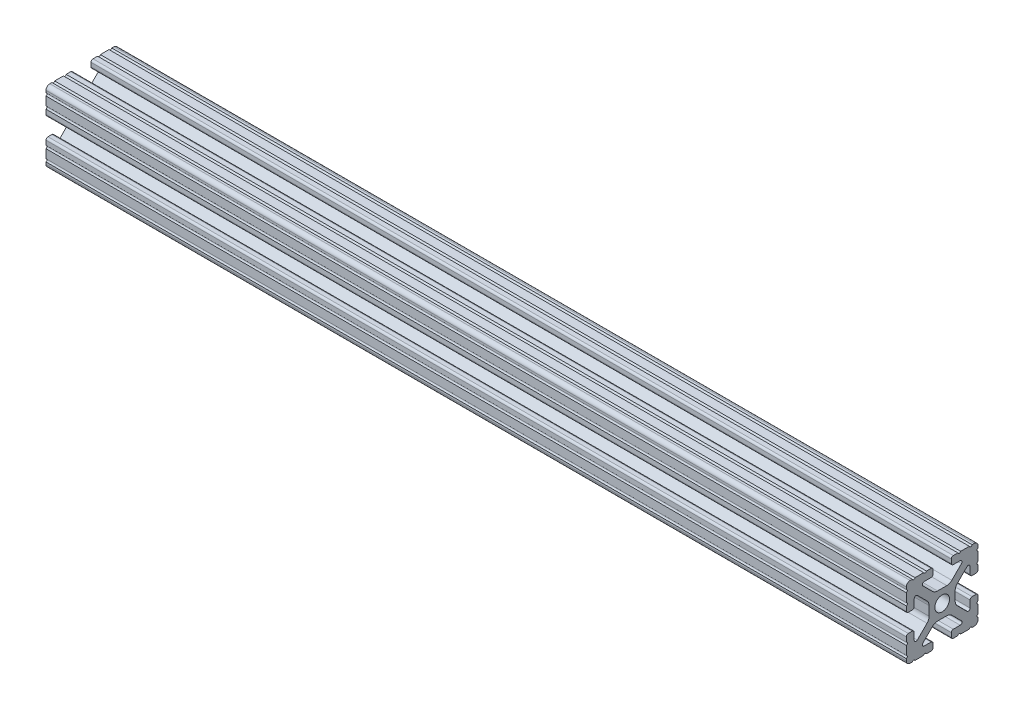
SolidWorks part; units mm, degrees
ref_plane "Front Plane" through (0, 0, 0) normal (0, 0, 1) x (1, 0, 0)
ref_plane "Top Plane" through (0, 0, 0) normal (0, 1, 0) x (1, 0, 0)
ref_plane "Right Plane" through (0, 0, 0) normal (1, 0, 0) x (0, 0, -1)
sketch "Sketch3"
sketch "Sketch2" plane through (0, 0, 0) normal (1, 0, 0) x (0, 0, -1)
  line L0 (16.1207, 7.3347) -> (19.544, 3.9114)
  line L1 (17.3256, 11.0651) -> (17.3256, 14.3349)
  line L2 (18.0653, 16.1207) -> (21.4886, 19.544)
  line L3 (22.598, 16.6362) -> (22.598, 19.0845)
  line L4 (24.7023, 15.9385) -> (23.2956, 15.9385)
  line L6 (2.1006, 25.4) -> (1.3474, 25.4)
  line L7 (16.6362, 2.802) -> (19.0845, 2.802)
  line L8 (0.6977, 15.9385) -> (2.1044, 15.9385)
  line L9 (2.802, 16.6362) -> (2.802, 19.0845)
  line L10 (0, 16.6362) -> (0, 18.2699)
  line L11 (8.0744, 11.0651) -> (8.0744, 14.3349)
  line L12 (7.3347, 16.1207) -> (3.9114, 19.544)
  line L13 (0, 19.2426) -> (0, 22.318)
  line L14 (0, 23.2994) -> (0, 24.0526)
  line L15 (6.1574, 25.4) -> (3.082, 25.4)
  line L16 (8.7638, 25.4) -> (7.1301, 25.4)
  line L17 (9.4615, 24.7023) -> (9.4615, 23.2956)
  line L18 (8.7638, 22.598) -> (6.3155, 22.598)
  line L19 (9.2793, 18.0653) -> (5.856, 21.4886)
  line L20 (14.3349, 17.3256) -> (11.0651, 17.3256)
  line L22 (25.4, 16.6362) -> (25.4, 18.2699)
  line L23 (25.4, 19.2426) -> (25.4, 22.318)
  line L24 (25.4, 23.2994) -> (25.4, 24.0526)
  line L25 (23.2994, 25.4) -> (24.0526, 25.4)
  line L26 (19.2426, 25.4) -> (22.318, 25.4)
  line L27 (16.6362, 25.4) -> (18.2699, 25.4)
  line L28 (15.9385, 24.7023) -> (15.9385, 23.2956)
  line L29 (16.6362, 22.598) -> (19.0845, 22.598)
  line L30 (16.1207, 18.0653) -> (19.544, 21.4886)
  line L31 (15.9385, 0.6977) -> (15.9385, 2.1044)
  line L32 (16.6362, 0) -> (18.2699, 0)
  line L33 (19.2426, 0) -> (22.318, 0)
  line L34 (23.2994, 0) -> (24.0526, 0)
  line L35 (25.4, 2.1006) -> (25.4, 1.3474)
  line L36 (25.4, 6.1574) -> (25.4, 3.082)
  line L37 (25.4, 8.7638) -> (25.4, 7.1301)
  line L38 (14.3349, 8.0744) -> (11.0651, 8.0744)
  line L39 (9.2793, 7.3347) -> (5.856, 3.9114)
  line L40 (8.7638, 2.802) -> (6.3155, 2.802)
  line L41 (9.4615, 0.6977) -> (9.4615, 2.1044)
  line L42 (8.7638, 0) -> (7.1301, 0)
  line L43 (6.1574, 0) -> (3.082, 0)
  line L44 (0, 2.1006) -> (0, 1.3474)
  line L45 (0, 6.1574) -> (0, 3.082)
  line L46 (7.3347, 9.2793) -> (3.9114, 5.856)
  line L47 (0, 8.7638) -> (0, 7.1301)
  line L48 (2.802, 8.7638) -> (2.802, 6.3155)
  line L49 (0.6977, 9.4615) -> (2.1044, 9.4615)
  line L50 (2.1006, 0) -> (1.3474, 0)
  line L51 (24.7023, 9.4615) -> (23.2956, 9.4615)
  line L52 (22.598, 8.7638) -> (22.598, 6.3155)
  line L53 (18.0653, 9.2793) -> (21.4886, 5.856)
  circle A0 centre (12.7, 12.7) radius 2.6035
  arc A1 (7.3347, 16.1207) -> (8.0744, 14.3349) centre (5.5489, 14.3349) cw
  arc A2 (2.802, 19.0845) -> (3.9114, 19.544) centre (3.4519, 19.0845) cw
  arc A3 (2.802, 16.6362) -> (2.1044, 15.9385) centre (2.1044, 16.6362) cw
  arc A4 (0, 16.6362) -> (0.6977, 15.9385) centre (0.6977, 16.6362) ccw
  arc A5 (-0.0204, 18.2642) -> (-0.0101, 19.2455) centre (-0.1467, 18.7562) ccw
  arc A6 (0, 22.318) -> (0, 23.2994) centre (-0.1315, 22.8087) ccw
  arc A7 (0, 24.0526) -> (1.3474, 25.4) centre (1.3474, 24.0526) cw
  arc A8 (3.082, 25.4) -> (2.1006, 25.4) centre (2.5913, 25.5315) cw
  arc A9 (7.1358, 25.4204) -> (6.1545, 25.4101) centre (6.6438, 25.5467) cw
  arc A10 (8.7638, 25.4) -> (9.4615, 24.7023) centre (8.7638, 24.7023) cw
  arc A11 (8.7638, 22.598) -> (9.4615, 23.2956) centre (8.7638, 23.2956) ccw
  arc A12 (6.3155, 22.598) -> (5.856, 21.4886) centre (6.3155, 21.9481) ccw
  arc A13 (9.2793, 18.0653) -> (11.0651, 17.3256) centre (11.0651, 19.8511) ccw
  arc A14 (18.0653, 16.1207) -> (17.3256, 14.3349) centre (19.8511, 14.3349) ccw
  arc A15 (22.598, 19.0845) -> (21.4886, 19.544) centre (21.9481, 19.0845) ccw
  arc A16 (22.598, 16.6362) -> (23.2956, 15.9385) centre (23.2956, 16.6362) ccw
  arc A17 (25.4, 16.6362) -> (24.7023, 15.9385) centre (24.7023, 16.6362) cw
  arc A18 (25.4204, 18.2642) -> (25.4101, 19.2455) centre (25.5467, 18.7562) cw
  arc A19 (25.4, 22.318) -> (25.4, 23.2994) centre (25.5315, 22.8087) cw
  arc A20 (25.4, 24.0526) -> (24.0526, 25.4) centre (24.0526, 24.0526) ccw
  arc A21 (22.318, 25.4) -> (23.2994, 25.4) centre (22.8087, 25.5315) ccw
  arc A22 (18.2642, 25.4204) -> (19.2455, 25.4101) centre (18.7562, 25.5467) ccw
  arc A23 (16.6362, 25.4) -> (15.9385, 24.7023) centre (16.6362, 24.7023) ccw
  arc A24 (16.6362, 22.598) -> (15.9385, 23.2956) centre (16.6362, 23.2956) cw
  arc A25 (19.0845, 22.598) -> (19.544, 21.4886) centre (19.0845, 21.9481) cw
  arc A26 (16.1207, 18.0653) -> (14.3349, 17.3256) centre (14.3349, 19.8511) cw
  arc A27 (16.1207, 7.3347) -> (14.3349, 8.0744) centre (14.3349, 5.5489) ccw
  arc A28 (19.0845, 2.802) -> (19.544, 3.9114) centre (19.0845, 3.4519) ccw
  arc A29 (16.6362, 2.802) -> (15.9385, 2.1044) centre (16.6362, 2.1044) ccw
  arc A30 (16.6362, 0) -> (15.9385, 0.6977) centre (16.6362, 0.6977) cw
  arc A31 (18.2642, -0.0204) -> (19.2455, -0.0101) centre (18.7562, -0.1467) cw
  arc A32 (22.318, 0) -> (23.2994, 0) centre (22.8087, -0.1315) cw
  arc A33 (25.4, 1.3474) -> (24.0526, 0) centre (24.0526, 1.3474) cw
  arc A34 (25.4, 3.082) -> (25.4, 2.1006) centre (25.5315, 2.5913) ccw
  arc A35 (25.4204, 7.1358) -> (25.4101, 6.1545) centre (25.5467, 6.6438) ccw
  arc A36 (25.4, 8.7638) -> (24.7023, 9.4615) centre (24.7023, 8.7638) ccw
  arc A37 (22.598, 8.7638) -> (23.2956, 9.4615) centre (23.2956, 8.7638) cw
  arc A38 (22.598, 6.3155) -> (21.4886, 5.856) centre (21.9481, 6.3155) cw
  arc A39 (18.0653, 9.2793) -> (17.3256, 11.0651) centre (19.8511, 11.0651) cw
  arc A40 (9.2793, 7.3347) -> (11.0651, 8.0744) centre (11.0651, 5.5489) cw
  arc A41 (6.3155, 2.802) -> (5.856, 3.9114) centre (6.3155, 3.4519) cw
  arc A42 (8.7638, 2.802) -> (9.4615, 2.1044) centre (8.7638, 2.1044) cw
  arc A43 (8.7638, 0) -> (9.4615, 0.6977) centre (8.7638, 0.6977) ccw
  arc A44 (7.1358, -0.0204) -> (6.1545, -0.0101) centre (6.6438, -0.1467) ccw
  arc A45 (3.082, 0) -> (2.1006, 0) centre (2.5913, -0.1315) ccw
  arc A46 (0, 1.3474) -> (1.3474, 0) centre (1.3474, 1.3474) ccw
  arc A47 (0, 3.082) -> (0, 2.1006) centre (-0.1315, 2.5913) cw
  arc A48 (-0.0204, 7.1358) -> (-0.0101, 6.1545) centre (-0.1467, 6.6438) cw
  arc A49 (0, 8.7638) -> (0.6977, 9.4615) centre (0.6977, 8.7638) cw
  arc A50 (2.802, 8.7638) -> (2.1044, 9.4615) centre (2.1044, 8.7638) ccw
  arc A51 (2.802, 6.3155) -> (3.9114, 5.856) centre (3.4519, 6.3155) ccw
  arc A52 (7.3347, 9.2793) -> (8.0744, 11.0651) centre (5.5489, 11.0651) ccw
  point P100 (12.7, 17.3256)
  point P181 (8.0744, 12.7)
  point P182 (17.3256, 12.7)
extrude "Boss-Extrude1" add sketch "Sketch2" along normal blind 304.8 contours A52 L46 A51 L48 A50 L49 A49 L47 A48 L45 A47 L44 A46 L50 A45 L43 A44 L42 A43 L41 A42 L40 A41 L39 A40 L38 A27 L0 A28 L7 A29 L31 A30 L32 A31 L33 A32 L34 A33 L35 A34 L36 A35 L37 A36 L51 A37 L52 A38 L53 A39
move or copy body "Body-Move/Copy1" bodies to move or copy 102 copy no translate (-150.0587, 28.7597, 59.645)
sketch "Sketch4" plane through (0, 0, 0) normal (0, 0, 1) x (1, 0, 0)
  line L0 (154.7413, 54.1597) -> (-150.0587, 54.1597) construction
  line L1 (-78.6761, 54.1597) -> (-106.0407, -11.9043)
  line L2 (378.5239, 54.1597) -> (405.8885, -11.9043)
  line L3 (405.8885, -11.9043) -> (480.3446, -42.745)
  line L4 (480.3446, -42.745) -> (535.2221, 89.7411)
  line L5 (535.2221, 89.7411) -> (378.5239, 89.7411)
  line L6 (378.5239, 89.7411) -> (378.5239, 54.1597)
  line L7 (-78.6761, 54.1597) -> (-78.6761, 92.6727)
  line L8 (-78.6761, 92.6727) -> (-197.9311, 43.2757)
  line L9 (-197.9311, 43.2757) -> (-164.965, -36.3115)
  line L10 (-164.965, -36.3115) -> (-106.0407, -11.9043)
  dimension "D1" = 67.5
  dimension "D2" = 67.5
